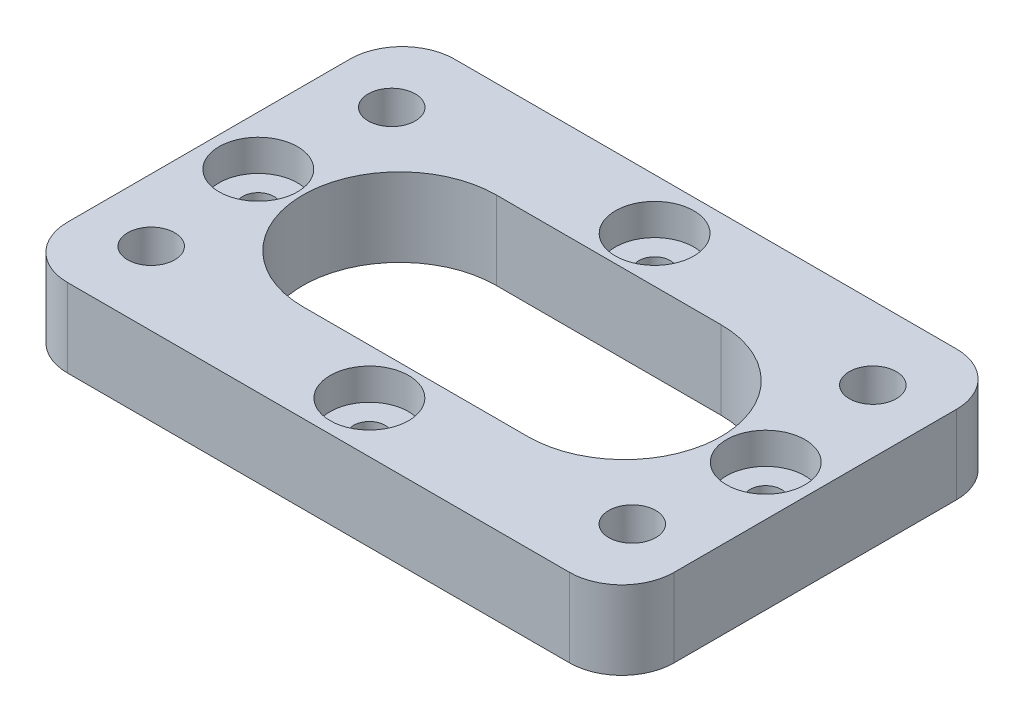
SolidWorks part; units mm, degrees
ref_plane "Front Plane" through (0, 0, 0) normal (0, 0, 1) x (1, 0, 0)
ref_plane "Top Plane" through (0, 0, 0) normal (0, 1, 0) x (1, 0, 0)
ref_plane "Right Plane" through (0, 0, 0) normal (1, 0, 0) x (0, 0, -1)
sketch "Sketch1" plane through (0, 0, 0) normal (0, 1, 0) x (1, 0, 0)
  line L0 (0, 37) -> (36.5, 37)
  line L1 (0, 0) -> (116, 0)
  line L2 (0, 0) -> (0, 74)
  line L3 (0, 74) -> (116, 74)
  line L4 (116, 0) -> (116, 74)
  line L5 (116, 37) -> (79.5, 37)
  line L6 (36.5, 55.5) -> (79.5, 55.5)
  line L7 (79.5, 55.5) -> (79.5, 18.5)
  line L8 (79.5, 18.5) -> (36.5, 18.5)
  line L9 (36.5, 18.5) -> (36.5, 55.5)
  circle A0 centre (36.5, 37) radius 18.5
  circle A1 centre (79.5, 37) radius 18.5
  dimension "D1" = 116
  dimension "D2" = 74
extrude "Boss-Extrude1" add sketch "Sketch1" along normal blind 15 contours L2 L1 L4 L3
sketch "Sketch2" plane through (0, 15, 0) normal (0, 1, 0) x (1, 0, 0)
  line L0 (0, 37) -> (36.5, 37)
  line L1 (0, 0) -> (0, 74) construction
  line L2 (116, 37) -> (79.5, 37)
  line L3 (116, 0) -> (116, 74) construction
  line L4 (36.5, 55.5) -> (79.5, 55.5)
  line L6 (79.5, 18.5) -> (36.5, 18.5)
  circle A0 centre (36.5, 37) radius 18.5
  circle A1 centre (79.5, 37) radius 18.5
extrude "Cut-Extrude1" cut sketch "Sketch2" against normal blind 15
sketch "Sketch4" plane through (0, 15, 0) normal (0, 1, 0) x (1, 0, 0)
  line L0 (0, 74) -> (12, 74)
  line L1 (0, 74) -> (116, 74) construction
  line L2 (12, 74) -> (12, 60)
  line L3 (0, 0) -> (12, 0)
  line L4 (0, 0) -> (116, 0) construction
  line L5 (12, 0) -> (12, 14)
  line L6 (116, 74) -> (104, 74)
  line L7 (104, 74) -> (104, 60)
  line L8 (116, 0) -> (104, 0)
  line L9 (104, 0) -> (104, 14)
  circle A0 centre (12, 60) radius 4.5
  circle A1 centre (12, 14) radius 4.5
  circle A2 centre (104, 60) radius 4.5
  circle A3 centre (104, 14) radius 4.5
  point P24 (0, 0)
extrude "Cut-Extrude2" cut sketch "Sketch4" against normal blind 15
sketch "Sketch5" plane through (0, 15, 0) normal (0, 1, 0) x (1, 0, 0)
  line L0 (18, 37) -> (9.48, 37)
  line L1 (98, 37) -> (106.52, 37)
  line L2 (58, 55.5) -> (58, 64.27)
  line L3 (36.5, 55.5) -> (79.5, 55.5) construction
  line L4 (58, 18.5) -> (58, 9.73)
  line L5 (79.5, 18.5) -> (36.5, 18.5) construction
  arc A0 (36.5, 55.5) -> (36.5, 18.5) centre (36.5, 37) ccw construction
  arc A1 (79.5, 18.5) -> (79.5, 55.5) centre (79.5, 37) ccw construction
  circle A2 centre (9.48, 37) radius 3
  circle A3 centre (58, 64.27) radius 3
  circle A4 centre (106.52, 37) radius 3
  circle A5 centre (58, 9.73) radius 3
extrude "Cut-Extrude3" cut sketch "Sketch5" against normal blind 15
sketch "Sketch6" plane through (0, 15, 0) normal (0, 1, 0) x (1, 0, 0)
  circle A0 centre (58, 64.27) radius 7.5
  circle A1 centre (9.48, 37) radius 7.5
  circle A2 centre (106.52, 37) radius 7.5
  circle A3 centre (58, 9.73) radius 7.5
extrude "Cut-Extrude4" cut sketch "Sketch6" against normal blind 6
sketch "Sketch8" plane through (0, 0, 0) normal (0, -1, 0) x (-1, 0, 0)
  line L31 (-13.9799, 21.3892) -> (-19.3892, 15.9799)
  line L32 (-19.3892, 15.9799) -> (-17.4093, 8.5907)
  line L33 (-17.4093, 8.5907) -> (-10.0201, 6.6108)
  line L34 (-10.0201, 6.6108) -> (-4.6108, 12.0201)
  line L35 (-4.6108, 12.0201) -> (-6.5907, 19.4093)
  line L36 (-6.5907, 19.4093) -> (-13.9799, 21.3892)
  line L37 (-96.5773, 15.8507) -> (-101.8914, 21.3535)
  line L38 (-101.8914, 21.3535) -> (-109.3141, 19.5029)
  line L39 (-109.3141, 19.5029) -> (-111.4227, 12.1493)
  line L40 (-111.4227, 12.1493) -> (-106.1086, 6.6465)
  line L41 (-106.1086, 6.6465) -> (-98.6859, 8.4971)
  line L42 (-98.6859, 8.4971) -> (-96.5773, 15.8507)
  line L43 (-102.5403, 52.4907) -> (-96.7669, 57.5094)
  line L44 (-96.7669, 57.5094) -> (-98.2266, 65.0188)
  line L45 (-98.2266, 65.0188) -> (-105.4597, 67.5093)
  line L46 (-105.4597, 67.5093) -> (-111.2331, 62.4906)
  line L47 (-111.2331, 62.4906) -> (-109.7734, 54.9812)
  line L48 (-109.7734, 54.9812) -> (-102.5403, 52.4907)
  line L49 (-19.2755, 57.6361) -> (-13.5905, 52.5173)
  line L50 (-13.5905, 52.5173) -> (-6.315, 54.8812)
  line L51 (-6.315, 54.8812) -> (-4.7245, 62.3639)
  line L52 (-4.7245, 62.3639) -> (-10.4095, 67.4827)
  line L53 (-10.4095, 67.4827) -> (-17.685, 65.1188)
  line L54 (-17.685, 65.1188) -> (-19.2755, 57.6361)
  circle A0 centre (-12, 14) radius 6.625 construction
  circle A1 centre (-104, 14) radius 6.625 construction
  circle A2 centre (-104, 60) radius 6.625 construction
  circle A3 centre (-12, 60) radius 6.625 construction
extrude "Cut-Extrude5" cut sketch "Sketch8" against normal blind 8
fillet "Fillet1" radius 10 3 edges at (116, 7.5, -74) (116, 7.5, 0) (0, 7.5, 0)
fillet "Fillet2" radius 10 1 edges at (0, 7.5, -74)
